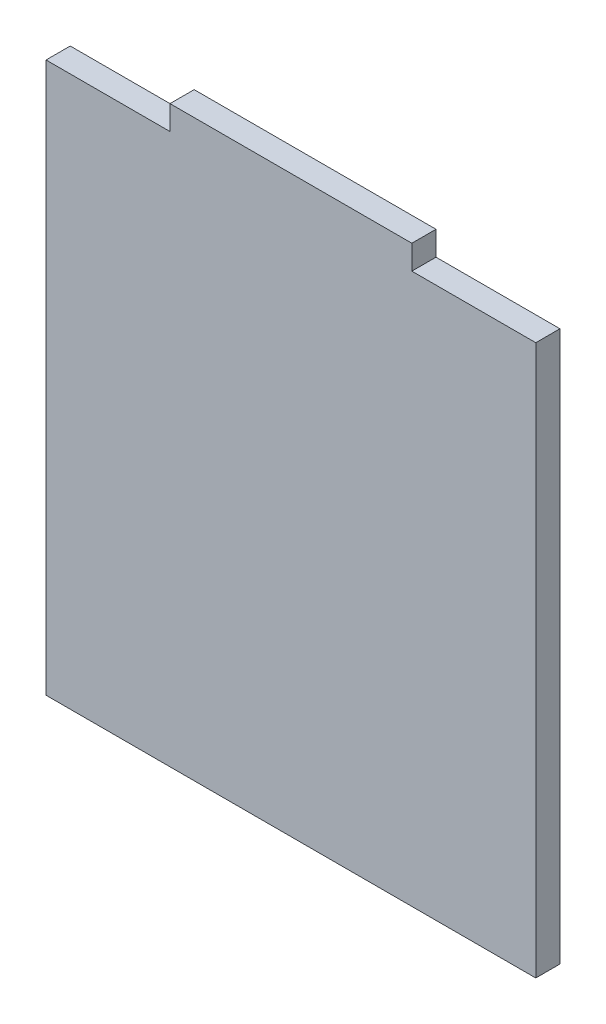
SolidWorks part; units mm, degrees
ref_plane "Front Plane" through (0, 0, 0) normal (0, 0, 1) x (1, 0, 0)
ref_plane "Top Plane" through (0, 0, 0) normal (0, 1, 0) x (1, 0, 0)
ref_plane "Right Plane" through (0, 0, 0) normal (1, 0, 0) x (0, 0, -1)
sketch "Sketch2" plane through (0, 0, 0) normal (0, 0, 1) x (1, 0, 0)
  line L1 (-64.2938, -72.2313) -> (64.2937, -72.2313)
  line L2 (-64.2938, -72.2313) -> (-64.2938, 72.2312)
  line L3 (-64.2938, 72.2312) -> (64.2937, 72.2312)
  line L4 (64.2937, -72.2313) -> (64.2937, 72.2312)
  line L5 (-64.2938, -72.2313) -> (64.2937, 72.2312) construction
  line L6 (-64.2938, 72.2312) -> (64.2937, -72.2313) construction
  point P0 (0, 0)
  dimension "D1" = 128.5875
  dimension "D2" = 144.4625
extrude "Boss-Extrude1" add sketch "Sketch2" along normal blind 6.35
sketch "Sketch3" plane through (0, 0, 6.35) normal (0, 0, 1) x (1, 0, 0)
  line L0 (64.2937, 72.2312) -> (-64.2938, 72.2312) construction
  line L1 (-31.75, 72.2312) -> (31.75, 72.2312)
  line L2 (-31.75, 72.2312) -> (-31.75, 78.5812)
  line L3 (-31.75, 78.5812) -> (31.75, 78.5812)
  line L4 (31.75, 72.2312) -> (31.75, 78.5812)
  line L5 (64.2937, -72.2313) -> (64.2937, 72.2312) construction
  dimension "D1" = 63.5
  dimension "D2" = 32.5437
  dimension "D3" = 6.35
extrude "Boss-Extrude2" add sketch "Sketch3" against normal blind 6.35
equation "\"width\"= 5.5625in"
equation "\"height\"= 6.1875in"
equation "\"shell\"= 0.25in"
equation "\"extrude\"= 0.5in"
equation "\"D1@Boss-Extrude1\"=\"extrude\""
equation "\"D1@Shell1\"=\"shell\""
